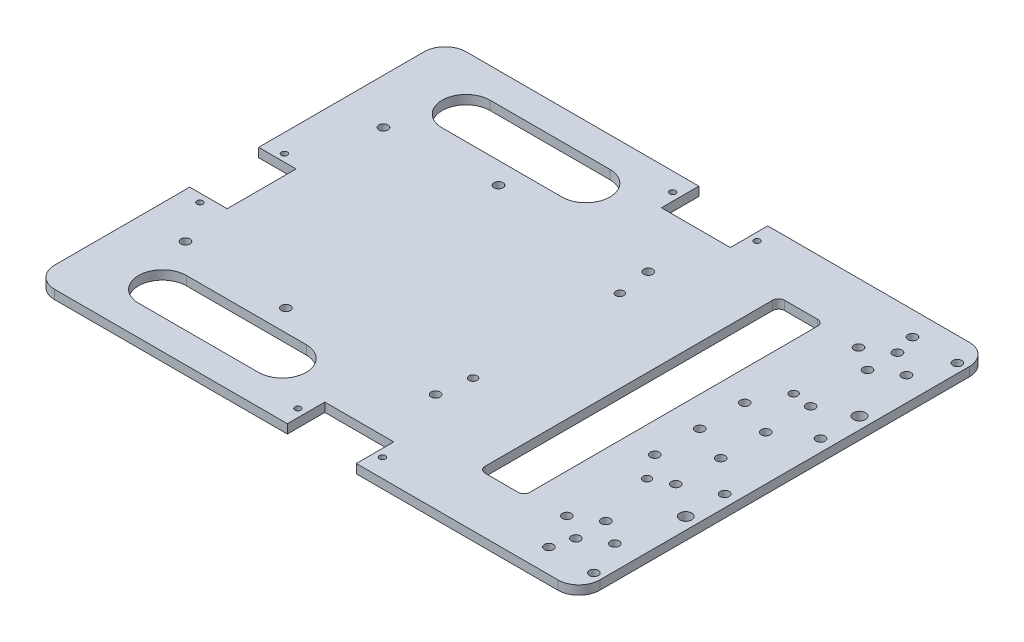
SolidWorks part; units mm, degrees
ref_plane "Front Plane" through (0, 0, 0) normal (0, 0, 1) x (1, 0, 0)
ref_plane "Top Plane" through (0, 0, 0) normal (0, 1, 0) x (1, 0, 0)
ref_plane "Right Plane" through (0, 0, 0) normal (1, 0, 0) x (0, 0, -1)
sketch "Sketch1" plane through (0, 0, 0) normal (0, 1, 0) x (1, 0, 0)
  line L1 (-82.9318, 1082.5636) -> (99.0682, 1082.5636)
  line L2 (-82.9318, 1082.5636) -> (-82.9318, 945.2036)
  line L3 (-82.9318, 945.2036) -> (99.0682, 945.2036)
  line L4 (99.0682, 1082.5636) -> (99.0682, 945.2036)
  dimension "D1" = 137.36
  dimension "D2" = 182
extrude "Boss-Extrude1" add sketch "Sketch1" along normal blind 3
sketch "Sketch2" plane through (0, 0, 0) normal (0, -1, 0) x (1, 0, 0)
  line L0 (-82.9318, -945.2036) -> (99.0682, -945.2036) construction
  line L1 (99.0682, -1082.5636) -> (-82.9318, -1082.5636) construction
  line L2 (99.0682, -945.2036) -> (99.0682, -1082.5636) construction
  circle A0 centre (95.0682, -1029.8836) radius 1.5
  circle A1 centre (95.0682, -997.8836) radius 1.5
  dimension "D1" = 3
  dimension "D2" = 3
  dimension "D3" = 52.68
  dimension "D4" = 52.68
  dimension "D5" = 4
  dimension "D6" = 4
extrude "Cut-Extrude1" cut sketch "Sketch2" against normal through all
sketch "Sketch3" plane through (0, 3, 0) normal (0, 1, 0) x (1, 0, 0)
  line L0 (99.0682, 1082.5636) -> (-82.9318, 1082.5636) construction
  line L1 (99.0682, 945.2036) -> (99.0682, 1082.5636) construction
  circle A0 centre (27.3282, 1076.4236) radius 1
  circle A1 centre (-0.8718, 1076.4236) radius 1
  circle A2 centre (-0.8718, 951.3636) radius 1
  circle A3 centre (27.3282, 951.3636) radius 1
  dimension "D1" = 2
  dimension "D2" = 6.14
  dimension "D3" = 71.74
  dimension "D4" = 2
  dimension "D5" = 2
extrude "Cut-Extrude2" cut sketch "Sketch3" against normal through all
sketch "Sketch4" plane through (0, 3, 0) normal (0, 1, 0) x (1, 0, 0)
  line L0 (-82.9318, 945.2036) -> (99.0682, 945.2036) construction
  line L1 (24.7682, 945.2036) -> (1.7682, 945.2036)
  line L2 (24.7682, 945.2036) -> (24.7682, 957.7036)
  line L3 (24.7682, 957.7036) -> (1.7682, 957.7036)
  line L4 (1.7682, 945.2036) -> (1.7682, 957.7036)
  line L5 (99.0682, 1082.5636) -> (-82.9318, 1082.5636) construction
  line L6 (24.7682, 1082.5636) -> (1.7682, 1082.5636)
  line L7 (24.7682, 1082.5636) -> (24.7682, 1070.0636)
  line L8 (24.7682, 1070.0636) -> (1.7682, 1070.0636)
  line L9 (1.7682, 1082.5636) -> (1.7682, 1070.0636)
  line L11 (-82.9318, 1082.5636) -> (-82.9318, 945.2036) construction
  dimension "D1" = 84.7
  dimension "D2" = 23
  dimension "D3" = 12.5
  dimension "D4" = 12.5
  dimension "D5" = 84.7
  dimension "D6" = 23
extrude "Cut-Extrude3" cut sketch "Sketch4" against normal through all
sketch "Sketch5" plane through (0, 0, 0) normal (0, -1, 0) x (1, 0, 0)
  circle A0 centre (77.5682, -1038.3836) radius 1.35
  circle A1 centre (77.6682, -989.3436) radius 1.35
  circle A2 centre (19.5682, -1038.3836) radius 1.35
  circle A3 centre (19.5682, -989.3836) radius 1.35
  dimension "D1" = 2.7
  dimension "D2" = 2.7
  dimension "D3" = 2.7
  dimension "D4" = 2.7
extrude "Cut-Extrude4" cut sketch "Sketch5" against normal through all
sketch "Sketch6" plane through (0, 3, 0) normal (0, 1, 0) x (1, 0, 0)
  circle A0 centre (18.0628, 1049.3836) radius 1.5
  circle A1 centre (-31.9372, 1049.3836) radius 1.5
  circle A2 centre (-31.9372, 978.3874) radius 1.5
  circle A3 centre (18.0628, 978.3874) radius 1.5
extrude "Cut-Extrude5" cut sketch "Sketch6" against normal through all
sketch "Sketch7" plane through (0, 3, 0) normal (0, 1, 0) x (1, 0, 0)
  line L0 (99.0682, 945.2036) -> (99.0682, 1082.5636) construction
  line L1 (49.0682, 1063.8836) -> (60.0682, 1063.8836)
  line L2 (47.0682, 1061.8836) -> (47.0682, 965.8836)
  line L3 (49.0682, 963.8836) -> (60.0682, 963.8836)
  line L4 (62.0682, 1061.8836) -> (62.0682, 965.8836)
  line L6 (24.7682, 945.2036) -> (99.0682, 945.2036) construction
  line L12 (-17.9318, 1064.5636) -> (-57.9318, 1064.5636) construction
  line L13 (-17.9318, 1056.5636) -> (-57.9318, 1056.5636)
  line L14 (-17.9318, 1072.5636) -> (-57.9318, 1072.5636)
  line L15 (-17.9318, 963.2036) -> (-57.9318, 963.2036) construction
  line L16 (-17.9318, 955.2036) -> (-57.9318, 955.2036)
  line L17 (-17.9318, 971.2036) -> (-57.9318, 971.2036)
  line L18 (-82.9318, 945.2036) -> (1.7682, 945.2036) construction
  line L19 (1.7682, 1082.5636) -> (-82.9318, 1082.5636) construction
  line L20 (-82.9318, 1082.5636) -> (-82.9318, 945.2036) construction
  arc A0 (-17.9318, 1056.5636) -> (-17.9318, 1072.5636) centre (-17.9318, 1064.5636) ccw
  arc A1 (-57.9318, 1072.5636) -> (-57.9318, 1056.5636) centre (-57.9318, 1064.5636) ccw
  arc A2 (-17.9318, 955.2036) -> (-17.9318, 971.2036) centre (-17.9318, 963.2036) ccw
  arc A3 (-57.9318, 971.2036) -> (-57.9318, 955.2036) centre (-57.9318, 963.2036) ccw
  arc A4 (49.0682, 1063.8836) -> (47.0682, 1061.8836) centre (49.0682, 1061.8836) ccw
  arc A5 (62.0682, 1061.8836) -> (60.0682, 1063.8836) centre (60.0682, 1061.8836) ccw
  arc A6 (60.0682, 963.8836) -> (62.0682, 965.8836) centre (60.0682, 965.8836) ccw
  arc A7 (49.0682, 963.8836) -> (47.0682, 965.8836) centre (49.0682, 965.8836) cw
  point P10 (47.0682, 1063.8836)
  point P18 (-37.9318, 1064.5636)
  point P23 (-37.9318, 963.2036)
  point P37 (47.0682, 963.8836)
  dimension "D9" = 8
  dimension "D10" = 8
  dimension "D17" = 2
  dimension "D6" = 2
  dimension "D7" = 2
  dimension "D8" = 2
  dimension "D2" = 37
  dimension "D3" = 15
  dimension "D4" = 100
  dimension "D5" = 18.68
  dimension "D11" = 10
  dimension "D12" = 10
  dimension "D13" = 40
  dimension "D14" = 40
  dimension "D15" = 25
  dimension "D16" = 25
extrude "Cut-Extrude6" cut sketch "Sketch7" against normal through all
fillet "Fillet1" radius 7 4 edges at (99.0682, 1.5, -1082.5636) (99.0682, 1.5, -945.2036) (-82.9318, 1.5, -1082.5636) (-82.9318, 1.5, -945.2036)
sketch "Sketch10" plane through (0, 3, 0) normal (0, 1, 0) x (1, 0, 0)
  circle A0 centre (96.0682, 1074.5636) radius 1.5
  circle A1 centre (81.0682, 1074.5636) radius 1.5
  circle A2 centre (81.0682, 953.2036) radius 1.5
  circle A3 centre (96.0682, 953.2036) radius 1.5
extrude "Cut-Extrude9" cut sketch "Sketch10" against normal through all
sketch "Sketch11" plane through (0, 0, 0) normal (0, -1, 0) x (1, 0, 0)
  circle A0 centre (-67.845, -1046.8836) radius 1.5
  circle A1 centre (-67.9318, -980.8836) radius 1.5
  dimension "D1" = 3
  dimension "D2" = 3
extrude "Cut-Extrude10" cut sketch "Sketch11" against normal through all
sketch "Sketch13" plane through (0, 0, 0) normal (0, -1, 0) x (1, 0, 0)
  line L0 (-82.9318, -1075.5636) -> (-82.9318, -952.2036) construction
  line L1 (-70.4318, -1020.3036) -> (-82.9318, -1020.3036)
  line L2 (-70.4318, -1020.3036) -> (-70.4318, -997.3036)
  line L3 (-70.4318, -997.3036) -> (-82.9318, -997.3036)
  line L4 (-82.9318, -1020.3036) -> (-82.9318, -997.3036)
  line L5 (-70.4318, -1020.3036) -> (-82.9318, -997.3036) construction
  line L6 (-70.4318, -997.3036) -> (-82.9318, -1020.3036) construction
  line L11 (1.7682, -1082.5636) -> (-75.9318, -1082.5636) construction
  point P0 (-76.6818, -1008.8036)
  dimension "D1" = 23
  dimension "D2" = 12.5
  dimension "D3" = 73.76
extrude "Cut-Extrude11" cut sketch "Sketch13" against normal up to next
sketch "Sketch14" plane through (0, 3, 0) normal (0, 1, 0) x (1, 0, 0)
  circle A0 centre (-76.787, 994.5536) radius 1
  circle A1 centre (-76.787, 1022.7536) radius 1
  dimension "D1" = 2
  dimension "D2" = 2
extrude "Cut-Extrude12" cut sketch "Sketch14" against normal through all
sketch "Sketch15" plane through (0, 0, 0) normal (0, -1, 0) x (1, 0, 0)
  circle A0 centre (95.0682, -1042.8836) radius 2
  circle A1 centre (95.0682, -984.8836) radius 2
extrude "Cut-Extrude13" cut sketch "Sketch15" against normal through all
sketch "Sketch16" plane through (0, 3, 0) normal (0, 1, 0) x (1, 0, 0)
  line L0 (24.7682, 945.2036) -> (92.0682, 945.2036) construction
  line L1 (99.0682, 952.2036) -> (99.0682, 1075.5636) construction
  line L2 (92.0682, 1082.5636) -> (24.7682, 1082.5636) construction
  line L3 (62.0682, 965.8836) -> (62.0682, 1061.8836) construction
  circle A0 centre (72.0682, 1027.5636) radius 1.5
  circle A1 centre (72.0682, 1012.5636) radius 1.5
  circle A2 centre (72.0682, 997.5636) radius 1.5
  circle A3 centre (84.0682, 1007.5636) radius 1.5
  circle A4 centre (84.0682, 1022.5636) radius 1.5
  circle A5 centre (84.0682, 1037.5636) radius 1.5
  circle A6 centre (75.0682, 1062.5636) radius 1.5
  circle A7 centre (91.0682, 1062.5636) radius 1.5
  circle A8 centre (83.0682, 1057.5636) radius 1.5
  circle A9 centre (83.0682, 1067.5636) radius 1.5
  circle A10 centre (91.0682, 965.2036) radius 1.5
  circle A11 centre (75.0682, 965.2036) radius 1.5
  circle A12 centre (83.0682, 970.2036) radius 1.5
  circle A13 centre (83.0682, 960.2036) radius 1.5
  circle A14 centre (84.0682, 992.5636) radius 1.5
  dimension "D1" = 15
  dimension "D2" = 20
  dimension "D3" = 20
  dimension "D4" = 25
  dimension "D5" = 3
  dimension "D6" = 3
  dimension "D7" = 3
  dimension "D8" = 3
  dimension "D10" = 16
  dimension "D11" = 16
  dimension "D12" = 24
  dimension "D13" = 3
  dimension "D14" = 3
  dimension "D15" = 3
  dimension "D16" = 3
  dimension "D17" = 15
  dimension "D18" = 20
  dimension "D19" = 20
  dimension "D20" = 25
  dimension "D21" = 8
  dimension "D22" = 16
  dimension "D23" = 16
  dimension "D24" = 24
  dimension "D25" = 3
  dimension "D26" = 3
  dimension "D27" = 3
  dimension "D28" = 3
  dimension "D29" = 3
  dimension "D30" = 3
  dimension "D31" = 15
  dimension "D32" = 15
  dimension "D34" = 10
  dimension "D35" = 10
  dimension "D36" = 10
  dimension "D37" = 15
  dimension "D38" = 15
  dimension "D39" = 15
  dimension "D40" = 15
  dimension "D41" = 45
  dimension "D42" = 55
  dimension "D43" = 15
  dimension "D44" = 3
  dimension "D45" = 15
  dimension "D9" = 8
  dimension "D33" = 15
extrude "Cut-Extrude14" cut sketch "Sketch16" against normal through all
